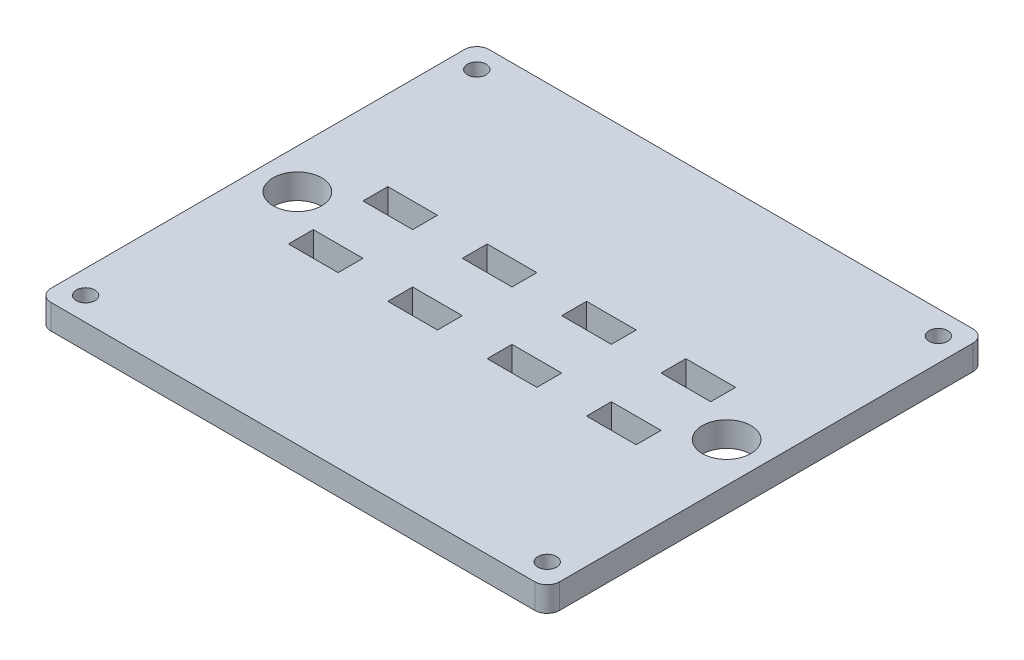
SolidWorks part; units mm, degrees
ref_plane "Front" through (0, 0, 0) normal (0, 0, 1) x (1, 0, 0)
ref_plane "Top" through (0, 0, 0) normal (0, 1, 0) x (1, 0, 0)
ref_plane "Right" through (0, 0, 0) normal (1, 0, 0) x (0, 0, -1)
sketch "Sketch1" plane through (0, 0, 0) normal (0, 1, 0) x (1, 0, 0)
  line L1 (0, 0) -> (65, 0)
  line L2 (0, 0) -> (0, 56)
  line L3 (0, 56) -> (65, 56)
  line L4 (65, 0) -> (65, 56)
  dimension "D1" = 65
  dimension "D2" = 56
extrude "Boss-Extrude1" add sketch "Sketch1" along normal blind 3.175
sketch "Sketch2" plane through (0, 3.175, 0) normal (0, 1, 0) x (1, 0, 0)
  line L0 (65, 0) -> (65, 56) construction
  line L1 (65, 56) -> (0, 56) construction
  line L2 (32.5, 56) -> (32.5, 0) construction
  line L3 (0, 0) -> (65, 0) construction
  line L4 (0, 28) -> (65, 28) construction
  line L5 (0, 56) -> (0, 0) construction
  line L6 (10.275, 34.35) -> (10.275, 31.175)
  line L7 (35.675, 34.35) -> (42.025, 34.35)
  line L8 (35.675, 34.35) -> (35.675, 31.175)
  line L9 (35.675, 31.175) -> (42.025, 31.175)
  line L10 (42.025, 34.35) -> (42.025, 31.175)
  line L11 (48.375, 34.35) -> (54.725, 34.35)
  line L12 (48.375, 34.35) -> (48.375, 31.175)
  line L13 (48.375, 31.175) -> (54.725, 31.175)
  line L14 (54.725, 34.35) -> (54.725, 31.175)
  line L15 (16.625, 31.175) -> (10.275, 31.175)
  line L16 (16.625, 34.35) -> (16.625, 31.175)
  line L17 (16.625, 34.35) -> (10.275, 34.35)
  line L18 (22.975, 34.35) -> (22.975, 31.175)
  line L19 (29.325, 31.175) -> (22.975, 31.175)
  line L20 (29.325, 34.35) -> (29.325, 31.175)
  line L21 (29.325, 34.35) -> (22.975, 34.35)
  line L22 (0, 28) -> (65, 28) construction
  line L23 (29.325, 21.65) -> (22.975, 21.65)
  line L24 (29.325, 21.65) -> (29.325, 24.825)
  line L25 (29.325, 24.825) -> (22.975, 24.825)
  line L26 (22.975, 21.65) -> (22.975, 24.825)
  line L27 (16.625, 21.65) -> (10.275, 21.65)
  line L28 (16.625, 21.65) -> (16.625, 24.825)
  line L29 (16.625, 24.825) -> (10.275, 24.825)
  line L30 (54.725, 21.65) -> (54.725, 24.825)
  line L31 (48.375, 24.825) -> (54.725, 24.825)
  line L32 (48.375, 21.65) -> (48.375, 24.825)
  line L33 (48.375, 21.65) -> (54.725, 21.65)
  line L34 (42.025, 21.65) -> (42.025, 24.825)
  line L35 (35.675, 24.825) -> (42.025, 24.825)
  line L36 (35.675, 21.65) -> (35.675, 24.825)
  line L37 (35.675, 21.65) -> (42.025, 21.65)
  line L38 (10.275, 21.65) -> (10.275, 24.825)
  circle A0 centre (62, 53) radius 1.1906
  circle A1 centre (3, 53) radius 1.1906
  circle A2 centre (3, 3) radius 1.1906
  circle A3 centre (62, 3) radius 1.1906
  dimension "D1" = 3
  dimension "D2" = 3
  dimension "D3" = 6.35
  dimension "D4" = 6.35
  dimension "D5" = 3.175
  dimension "D6" = 6.35
  dimension "D7" = 3.175
  dimension "D8" = 3.175
  dimension "D9" = 0
  dimension "D10" = 0
  dimension "D11" = 0
extrude "Cut-Extrude1" cut sketch "Sketch2" against normal blind 3.175
fillet "Fillet1" radius 1.5875 4 edges at (65, 1.5875, -56) (65, 1.5875, 0) (0, 1.5875, 0) (0, 1.5875, -56)
sketch "Sketch3" plane through (0, 3.175, 0) normal (0, 1, 0) x (1, 0, 0)
  line L0 (32.5, 56) -> (32.5, 0) construction
  line L1 (63.4125, 56) -> (1.5875, 56) construction
  line L2 (1.5875, 0) -> (63.4125, 0) construction
  circle A0 centre (5.068, 28) radius 3.1061
  circle A1 centre (59.932, 28) radius 3.1061
extrude "Cut-Extrude2" cut sketch "Sketch3" against normal blind 3.175
